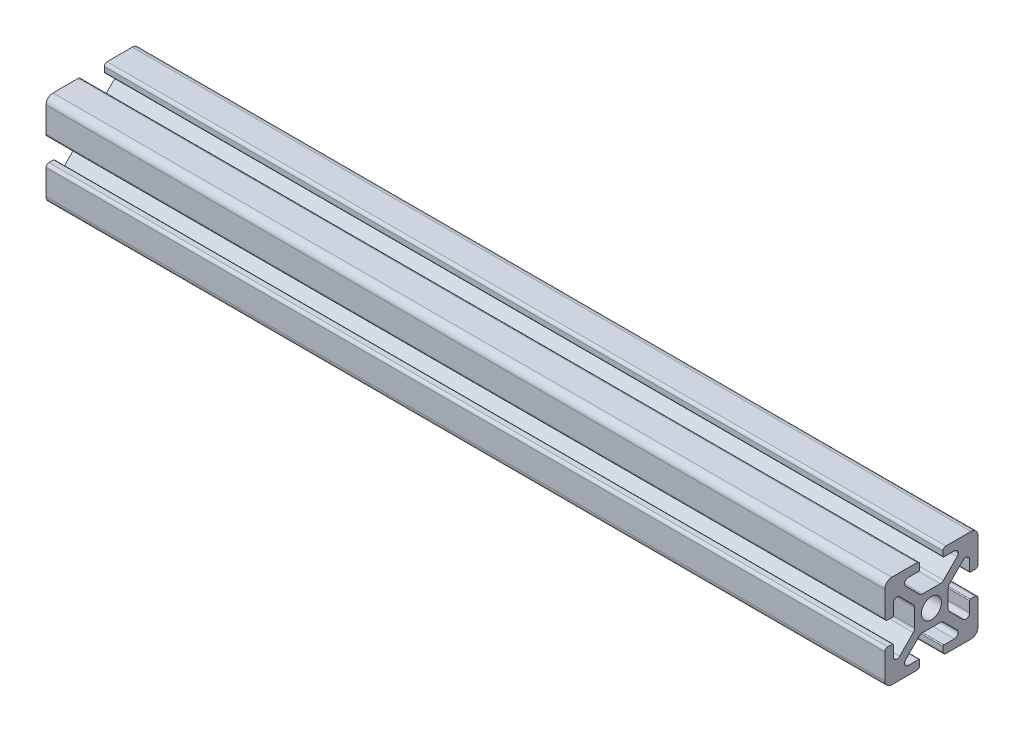
SolidWorks part; units mm, degrees
ref_plane "Front Plane" through (0, 0, 0) normal (0, 0, 1) x (1, 0, 0)
ref_plane "Top Plane" through (0, 0, 0) normal (0, 1, 0) x (1, 0, 0)
ref_plane "Right Plane" through (0, 0, 0) normal (1, 0, 0) x (0, 0, -1)
sketch "Sketch1" plane through (0, 0, 0) normal (1, 0, 0) x (0, 0, -1)
  line L0 (0, -10) -> (0, 10) construction
  line L1 (10, -10) -> (-10, -10)
  line L2 (10, -10) -> (10, 10)
  line L3 (10, 10) -> (0, 10)
  line L4 (-10, -10) -> (-10, 10)
  line L5 (10, -10) -> (-10, 10) construction
  line L6 (10, 10) -> (-10, -10) construction
  line L7 (10, 0) -> (-10, 0) construction
  line L8 (-2.5, 9.4) -> (-2.5, 8.3731)
  line L9 (-2.7, 8.1731) -> (-4.95, 8.1731)
  line L10 (-5.5157, 6.8075) -> (-2.6011, 3.8929)
  line L11 (-1.894, 3.6) -> (0, 3.6)
  line L12 (-5.3502, 4.0584) -> (-4.0584, 5.3502) construction
  line L13 (-3.825, 8.1731) -> (-3.825, 10) construction
  line L14 (-3.1, 10) -> (-10, 10)
  line L15 (-5.75, 7.3731) -> (5.75, 7.3731) construction
  circle A0 centre (0, 0) radius 2.15
  arc A1 (-4.95, 8.1731) -> (-5.5157, 6.8075) centre (-4.95, 7.3731) ccw
  arc A2 (-2.6011, 3.8929) -> (-1.894, 3.6) centre (-1.894, 4.6) ccw
  arc A3 (-2.5, 8.3731) -> (-2.7, 8.1731) centre (-2.7, 8.3731) cw
  arc A4 (-2.5, 9.4) -> (-3.1, 10) centre (-3.1, 9.4) ccw
  point P0 (0, 0)
  point P9 (0, 0)
  point P12 (0, 0)
  point P22 (-4.7043, 4.7043)
  point P32 (-2.5, 10)
  point P33 (-2.5, 8.8866)
  point P35 (-4.0584, 5.3502)
  point P37 (0, 7.3731)
  dimension "Center Hole Diameter" = 4.3
  dimension "D4" = 1
  dimension "D5" = 0.2
  dimension "D6" = 0.6
  dimension "D3" = 0.8
  dimension "Rail Height" = 20
  dimension "D7" = 6.4
  dimension "T Slot Width" = 5
  dimension "D10" = 10
  dimension "Rail Width" = 20
  dimension "D2" = 11.5
sketch "Sketch2" plane through (0, 0, 0) normal (0, 0, 1) x (1, 0, 0)
  line L0 (-132.4, 10) -> (-132.4, -10) construction
  line L1 (152.4, -10) -> (-152.4, -10) construction
  line L2 (152.4, -10) -> (152.4, 10) construction
  line L3 (152.4, 10) -> (-152.4, 10) construction
  line L4 (-152.4, -10) -> (-152.4, 10) construction
  line L5 (152.4, -10) -> (-152.4, 10) construction
  line L6 (152.4, 10) -> (-152.4, -10) construction
  line L7 (132.4, 10) -> (132.4, -10) construction
  point P0 (0, 0)
  point P12 (132.4, 0)
  dimension "Length" = 304.8
  dimension "D1" = 20
  dimension "D2" = 20
sketch "Sketch3" plane through (0, 0, 0) normal (1, 0, 0) x (0, 0, -1)
  line L0 (-5.5157, 6.8075) -> (-2.6011, 3.8929) construction
  line L5 (-3.1, 10) -> (-10, 10) construction
  line L6 (-2.5, 9.4) -> (-2.5, 8.3731) construction
  line L7 (-2.7, 8.1731) -> (-4.95, 8.1731) construction
  line L8 (-1.894, 3.6) -> (0, 3.6) construction
  line L9 (-5.5157, 6.8075) -> (-2.6011, 3.8929)
  line L10 (-10, 10) -> (0, 0) construction
  line L12 (-3.6, 1.894) -> (-3.6, 0)
  line L13 (-8.1731, 2.7) -> (-8.1731, 4.95)
  line L14 (-3.1, 10) -> (-8.5, 10)
  line L15 (-2.5, 9.4) -> (-2.5, 8.3731)
  line L16 (-2.7, 8.1731) -> (-4.95, 8.1731)
  line L17 (-1.894, 3.6) -> (0, 3.6)
  line L18 (-9.4, 2.5) -> (-8.3731, 2.5)
  line L19 (-10, 3.1) -> (-10, 8.5)
  line L20 (-6.8075, 5.5157) -> (-3.8929, 2.6011)
  line L21 (-3.6, 0) -> (-2.15, 0)
  line L22 (0, 3.6) -> (0, 2.15)
  arc A0 (-2.5, 9.4) -> (-3.1, 10) centre (-3.1, 9.4) ccw construction
  arc A1 (-2.7, 8.1731) -> (-2.5, 8.3731) centre (-2.7, 8.3731) ccw construction
  arc A2 (-4.95, 8.1731) -> (-5.5157, 6.8075) centre (-4.95, 7.3731) ccw construction
  arc A3 (-2.6011, 3.8929) -> (-1.894, 3.6) centre (-1.894, 4.6) ccw construction
  arc A4 (-2.5, 9.4) -> (-3.1, 10) centre (-3.1, 9.4) ccw
  arc A5 (-2.7, 8.1731) -> (-2.5, 8.3731) centre (-2.7, 8.3731) ccw
  arc A6 (-4.95, 8.1731) -> (-5.5157, 6.8075) centre (-4.95, 7.3731) ccw
  arc A7 (-2.6011, 3.8929) -> (-1.894, 3.6) centre (-1.894, 4.6) ccw
  arc A8 (-3.8929, 2.6011) -> (-3.6, 1.894) centre (-4.6, 1.894) cw
  arc A9 (-8.1731, 4.95) -> (-6.8075, 5.5157) centre (-7.3731, 4.95) cw
  arc A10 (-8.1731, 2.7) -> (-8.3731, 2.5) centre (-8.3731, 2.7) cw
  arc A11 (-9.4, 2.5) -> (-10, 3.1) centre (-9.4, 3.1) cw
  circle A12 centre (0, 0) radius 2.15 construction
  arc A13 (0, 2.15) -> (-2.15, 0) centre (0, 0) ccw
  arc A14 (-10, 8.5) -> (-8.5, 10) centre (-8.5, 8.5) cw
  dimension "D1" = 1.5
extrude "Boss-Extrude1" add sketch "Sketch3" against normal blind 180
mirror "Mirror1" about plane through (0, 0, 0) normal (0, 1, 0) of bodies 104
mirror "Mirror2" about plane through (0, 0, 0) normal (0, 0, 1) of bodies 105
equation "\"D10@Sketch1\" = \"Rail Height@Sketch1\" / 2"
equation "\"D2@Sketch2\"=\"D1@Sketch2\""
